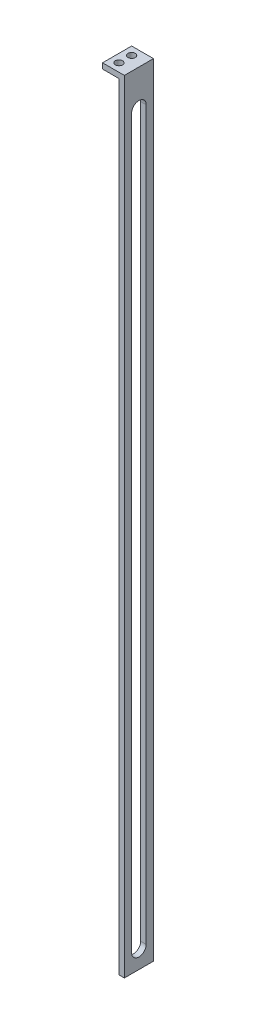
SolidWorks part; units mm, degrees
ref_plane "Front Plane" through (0, 0, 0) normal (0, 0, 1) x (1, 0, 0)
ref_plane "Top Plane" through (0, 0, 0) normal (0, 1, 0) x (1, 0, 0)
ref_plane "Right Plane" through (0, 0, 0) normal (1, 0, 0) x (0, 0, -1)
sketch "Sketch1" plane through (0, 0, 0) normal (0, 0, 1) x (1, 0, 0)
  line L0 (-96.6667, 109.1667) -> (-84.6667, 109.1667)
  line L1 (-84.6667, 109.1667) -> (-84.6667, -320.8333)
  line L2 (-84.6667, -320.8333) -> (-87.6667, -320.8333)
  line L3 (-87.6667, -320.8333) -> (-87.6667, 106.1667)
  line L4 (-87.6667, 106.1667) -> (-96.6667, 106.1667)
  line L5 (-96.6667, 106.1667) -> (-96.6667, 109.1667)
  dimension "D1" = 430
  dimension "D2" = 3
  dimension "D3" = 3
  dimension "D4" = 9
  dimension "D5" = 84.6667
  dimension "D6" = 109.1667
extrude "Boss-Extrude1" add sketch "Sketch1" along normal blind 16
sketch "Sketch2" plane through (0, 0, 0) normal (0, 1, 0) x (1, 0, 0)
  line L0 (-92.1667, -16) -> (-92.1667, 0) construction
  line L1 (-96.6667, -16) -> (-87.6667, -16) construction
  line L2 (-96.6667, 0) -> (-87.6667, 0) construction
  line L4 (-87.6667, -16) -> (-87.6667, 0) construction
  line L5 (-87.6667, -8) -> (-96.6667, -8) construction
  line L6 (-96.6667, -16) -> (-96.6667, 0) construction
  circle A0 centre (-92.1667, -11.5) radius 2
  circle A1 centre (-92.1667, -4.5) radius 2
  point P14 (-92.1667, -8)
  dimension "D1" = 4
  dimension "D2" = 3.5
extrude "Cut-Extrude1" cut sketch "Sketch2" against normal through all both and the other way through all
sketch "Sketch3" plane through (0, 0, 0) normal (1, 0, 0) x (0, 0, -1)
  line L0 (-8, 89.1667) -> (-8, -310.8333) construction
  line L1 (-4, 89.1667) -> (-4, -310.8333)
  line L2 (-12, 89.1667) -> (-12, -310.8333)
  line L4 (-16, 109.1667) -> (0, 109.1667) construction
  line L5 (-16, -320.8333) -> (-16, 109.1667) construction
  arc A0 (-4, 89.1667) -> (-12, 89.1667) centre (-8, 89.1667) ccw
  arc A1 (-12, -310.8333) -> (-4, -310.8333) centre (-8, -310.8333) ccw
  point P2 (-8, -110.8333)
  dimension "D2" = 4
  dimension "D3" = 20
  dimension "D1" = 400
  dimension "D4" = 8
extrude "Cut-Extrude2" cut sketch "Sketch3" against normal through all
